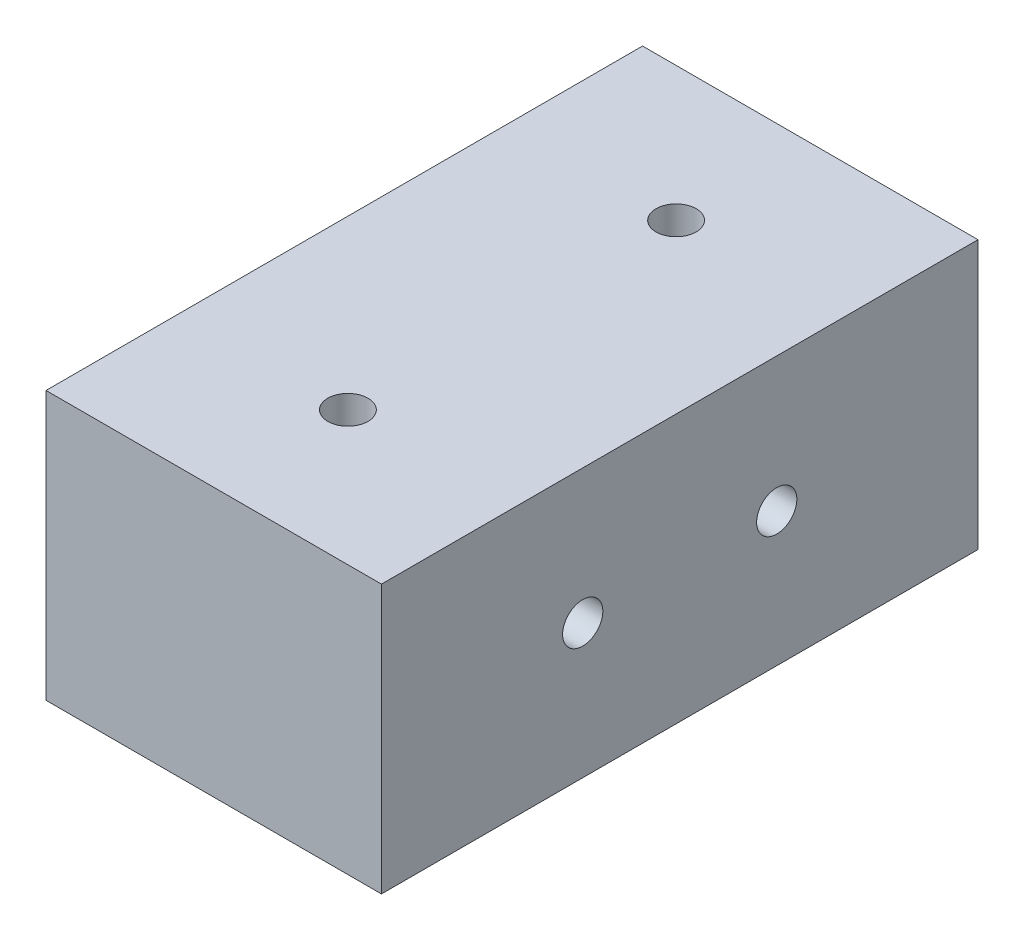
SolidWorks part; units mm, degrees
ref_plane "Alzado" through (0, 0, 0) normal (0, 0, 1) x (1, 0, 0)
ref_plane "Planta" through (0, 0, 0) normal (0, 1, 0) x (1, 0, 0)
ref_plane "Vista lateral" through (0, 0, 0) normal (1, 0, 0) x (0, 0, -1)
sketch "Croquis2" plane through (0, 0, 0) normal (1, 0, 0) x (0, 0, -1)
  line L0 (0, 0) -> (-44.4603, 0)
  line L1 (0, 0) -> (-50, 0) construction
  line L3 (0, -20) -> (-44.4603, -20)
  line L7 (0, -20) -> (0, 0)
  line L8 (-44.4603, -20) -> (-44.4603, 0)
  line L10 (-50, 0) -> (-75.7248, -15.4349) construction
  line L11 (-44.4603, -20) -> (-55.7248, -26.7587) construction
  line L12 (-55.7248, -26.7587) -> (-55.7248, -45.4349) construction
  line L13 (-75.7248, -15.4349) -> (-75.7248, -45.4349) construction
  dimension "D4" = 20
extrude "Saliente-Extruir2" add sketch "Croquis2" along normal blind 25
sketch "Croquis3" plane through (0, -20, 0) normal (0, -1, 0) x (1, 0, 0)
  line L0 (12.5, 0) -> (12.5, 44.4603) construction
  line L1 (25, 0) -> (0, 0) construction
  line L2 (25, 44.4603) -> (0, 44.4603) construction
  circle A0 centre (12.5, 10) radius 1.5
  circle A1 centre (12.5, 34.4603) radius 1.5
  dimension "D1" = 10
  dimension "D3" = 3
  dimension "D4" = 3
  dimension "D2" = 10
extrude "Cortar-Extruir1" cut sketch "Croquis3" against normal through all
sketch "Croquis4" plane through (25, 0, 0) normal (1, 0, 0) x (0, 0, -1)
  line L0 (-44.4603, -10) -> (0, -10) construction
  line L1 (-44.4603, 0) -> (-44.4603, -20) construction
  line L2 (0, -20) -> (0, 0) construction
  circle A0 centre (-29.4603, -10) radius 1.5
  circle A1 centre (-15, -10) radius 1.5
  dimension "D1" = 15
  dimension "D3" = 3
  dimension "D4" = 3
  dimension "D2" = 15
extrude "Cortar-Extruir2" cut sketch "Croquis4" against normal blind 50
